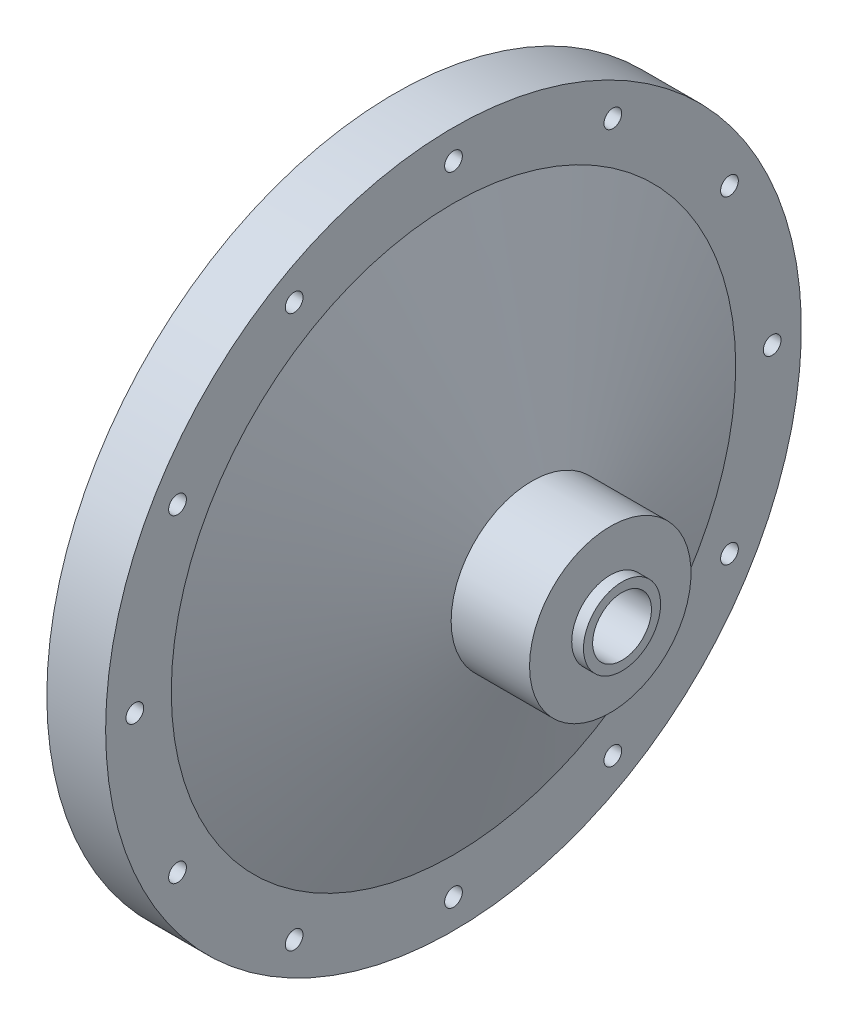
SolidWorks part; units mm, degrees
material "7075-T6 (SN)"
ref_plane "Front Plane" through (0, 0, 0) normal (0, 0, 1) x (1, 0, 0)
ref_plane "Top Plane" through (0, 0, 0) normal (0, 1, 0) x (1, 0, 0)
ref_plane "Right Plane" through (0, 0, 0) normal (1, 0, 0) x (0, 0, -1)
sketch "Sketch2" plane through (0, 0, 0) normal (0, 0, 1) x (1, 0, 0)
  line L0 (0, 0) -> (165.0115, 0) construction
  line L1 (0, 0) -> (0, 56.3562)
  line L2 (0, 56.3562) -> (9.525, 56.3562)
  line L3 (9.525, 56.3562) -> (9.525, 45.72)
  line L4 (9.525, 45.72) -> (22.225, 13.081)
  line L5 (34.925, 13.081) -> (34.925, 6.2484)
  line L6 (22.225, 13.081) -> (34.925, 13.081)
  line L7 (34.925, 6.2484) -> (36.83, 6.2484)
  line L8 (36.83, 6.2484) -> (36.83, 0)
  line L9 (0, 0) -> (36.83, 0)
  dimension "D1" = 56.3562
  dimension "D2" = 9.525
  dimension "D3" = 45.72
  dimension "D4" = 13.081
  dimension "D5" = 12.7
  dimension "D6" = 12.7
  dimension "D7" = 6.2484
  dimension "D8" = 1.905
revolve "Main Structure" add sketch "Sketch2" angle 360 about L0
cosmetic thread "Cosmetic Thread1" parameters "D2"=23.1953
sketch "Sketch3" plane through (36.83, 0, 0) normal (1, 0, 0) x (0, 0, -1)
  circle A0 centre (0, 0) radius 4.7625
  dimension "D1" = 9.525
extrude "Oxidizer Inlet Hole" cut sketch "Sketch3" against normal through all
sketch "Sketch4" plane through (0, 0, 0) normal (-1, 0, 0) x (0, 0, 1)
  circle A0 centre (0, 0) radius 51.6255 construction
  circle A1 centre (0, -51.6255) radius 2.146
  circle A2 centre (-25.8127, -44.709) radius 2.146
  circle A3 centre (-44.709, -25.8128) radius 2.146
  circle A4 centre (-51.6255, 0) radius 2.146
  circle A5 centre (-44.709, 25.8127) radius 2.146
  circle A6 centre (-25.8128, 44.709) radius 2.146
  circle A7 centre (0, 51.6255) radius 2.146
  circle A8 centre (25.8127, 44.709) radius 2.146
  circle A9 centre (44.709, 25.8128) radius 2.146
  circle A10 centre (51.6255, 0) radius 2.146
  circle A11 centre (44.709, -25.8127) radius 2.146
  circle A12 centre (25.8128, -44.709) radius 2.146
  point P29 (0, 0)
  dimension "D1" = 12
  dimension "D2" = 103.251
hole_wizard "Flange Holes" positions "Sketch7" profile "Sketch8" hole size "#33" standard "ANSI Inch" end condition up to next
sketch "Sketch7" plane through (0, 0, 0) normal (-1, 0, 0) x (0, 0, 1)
  point P0 (0, -51.6255)
  point P3 (-25.8127, -44.709)
  point P6 (-44.709, -25.8128)
  point P9 (-51.6255, 0)
  point P12 (-44.709, 25.8127)
  point P15 (-25.8128, 44.709)
  point P18 (0, 51.6255)
  point P21 (25.8127, 44.709)
  point P24 (44.709, 25.8128)
  point P27 (51.6255, 0)
  point P30 (44.709, -25.8127)
  point P33 (25.8128, -44.709)
sketch "Sketch8" plane through (0, -51.6255, 0) normal (0, 1, 0) x (0, 0, 1)
  line L0 (0, 0) -> (0, 9.525)
  line L1 (0, 9.525) -> (1.4351, 9.525)
  line L2 (1.4351, 9.525) -> (1.4351, 0)
  line L5 (1.4351, 0) -> (0, 0)
  line L11 (0, -6.35) -> (0, 107.95) construction
  dimension "Thru Hole Dia." = 2.8702
  dimension "Thru Hole Depth" = 9.525
sketch "Sketch9" plane through (0, 0, 0) normal (-1, 0, 0) x (0, 0, 1)
  line L0 (0, 0) -> (-67.6727, 18.1329) construction
  line L1 (0, 0) -> (-51.6255, 0) construction
  circle A0 centre (0, 0) radius 51.6255 construction
  circle A1 centre (-49.8664, 13.3617) radius 2.9451
  circle A2 centre (49.8664, -13.3617) radius 2.9451
  point P14 (0, 0)
  dimension "D1" = 15
  dimension "D2" = 2
hole_wizard "Dowel Holes" positions "Sketch10" profile "Sketch11" hole size "3/16" standard "ANSI Inch"
sketch "Sketch10" plane through (0, 0, 0) normal (-1, 0, 0) x (0, 0, 1)
  point P0 (49.8664, -13.3617)
  point P3 (-49.8664, 13.3617)
sketch "Sketch11" plane through (0, -13.3617, 49.8664) normal (0, 1, 0) x (0, 0, 1)
  line L0 (0, 0) -> (0, 7.7808)
  line L1 (0, 7.7808) -> (2.3812, 6.35)
  line L2 (2.3812, 6.35) -> (2.3812, 0)
  line L5 (2.3812, 0) -> (0, 0)
  line L10 (0, 7.7808) -> (-2.3812, 6.35) construction
  line L11 (0, -6.35) -> (0, 107.95) construction
  dimension "Hole Dia." = 4.7625
  dimension "Hole Depth" = 6.35
  dimension "Drill Angle" = 118
sketch "Sketch12" plane through (0, 0, 0) normal (-1, 0, 0) x (0, 0, 1)
  circle A0 centre (0, 0) radius 38.1
  dimension "D1" = 76.2
extrude "Impinging Plate Flat Cut" cut sketch "Sketch12" against normal blind 3.81
ref_plane "Plane1" through (6.35, 0, 0) normal (-1, 0, 0) x (0, 0, 1)
sketch "Sketch14" plane through (3.81, 0, 0) normal (-1, 0, 0) x (0, 0, 1)
  circle A0 centre (0, 0) radius 38.1
  dimension "D1" = 76.2
sketch "Sketch15" plane through (6.35, 0, 0) normal (-1, 0, 0) x (0, 0, 1)
  circle A0 centre (0, 0) radius 38.1
  dimension "D1" = 76.2
loft "Impinging Plate Taper Cut" cut profiles "Sketch14", "Sketch15"
sketch "Sketch16" plane through (6.35, 0, 0) normal (-1, 0, 0) x (0, 0, 1)
  circle A0 centre (0, 0) radius 28.575
  dimension "D1" = 57.15
ref_plane "Plane2" through (21.59, 0, 0) normal (-1, 0, 0) x (0, 0, 1)
sketch "Sketch17" plane through (21.59, 0, 0) normal (-1, 0, 0) x (0, 0, 1)
  circle A0 centre (0, 0) radius 4.7625
  dimension "D1" = 9.525
loft "Internal Flow Path Loft Cut" cut profiles "Sketch16", "Sketch17"
fillet "Internal Fillet" radius 3.175 1 edges at (21.59, 0, 4.7625)
sketch "Sketch18" plane through (6.35, 0, 0) normal (-1, 0, 0) x (0, 0, 1)
  circle A0 centre (0, 0) radius 33.3375
  circle A1 centre (33.3375, 0) radius 1.5042
  dimension "D1" = 66.675
hole_wizard "4-40 Tapped Holes " positions "Sketch19" profile "Sketch20" hole size "#4-40" standard "ANSI Inch"
sketch "Sketch19" plane through (6.35, 0, 0) normal (-1, 0, 0) x (0, 0, 1)
  point P0 (33.3375, 0)
sketch "Sketch20" plane through (6.35, 0, 33.3375) normal (0, 1, 0) x (0, 0, 1)
  line L0 (0, 0) -> (0, 3.8542)
  line L1 (0, 3.8542) -> (1.1303, 3.175)
  line L2 (1.1303, 3.175) -> (1.1303, 0)
  line L5 (1.1303, 0) -> (0, 0)
  line L10 (0, 3.8542) -> (-1.1303, 3.175) construction
  line L11 (0, -6.35) -> (0, 107.95) construction
  dimension "Hole Dia." = 2.2606
  dimension "Hole Depth" = 3.175
  dimension "Drill Angle" = 118
pattern_circular "Extended 8 BC" count 8 over 360 about axis through (0, 0, 0) along (1, 0, 0) of "4-40 Tapped Holes "
chamfer "Chamfer for Impinging Edge" distance 0.127 angle 45 1 edges at (6.35, 0, 38.1)
